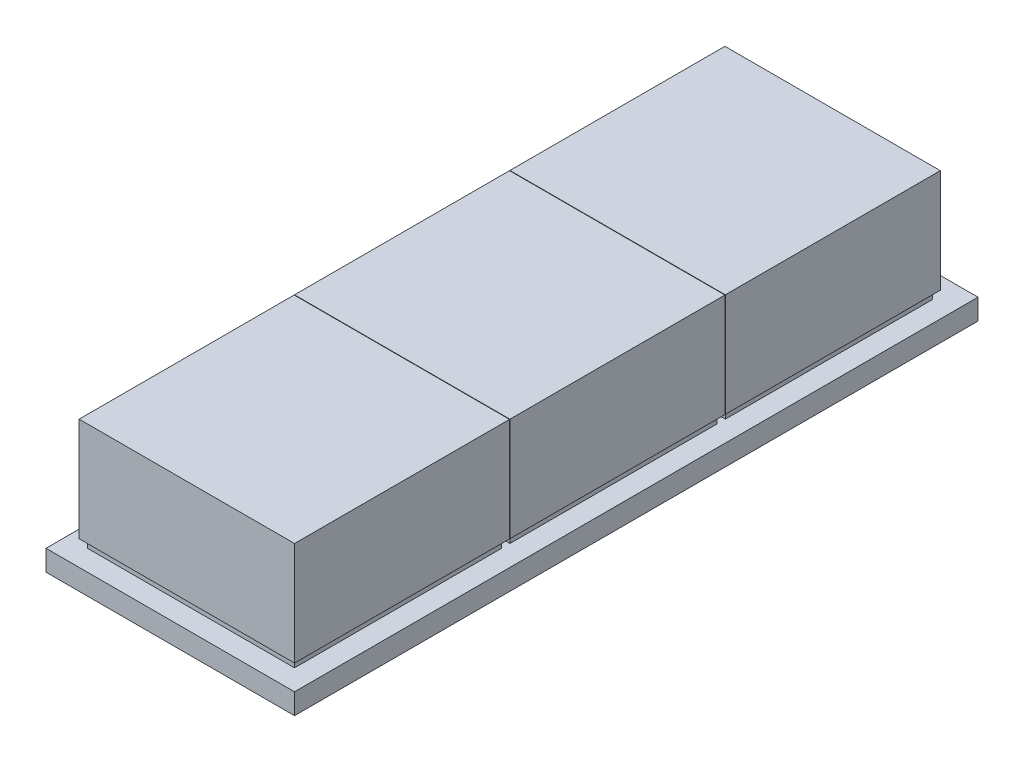
SolidWorks part; units mm, degrees
ref_plane "Front Plane" through (0, 0, 0) normal (0, 0, 1) x (1, 0, 0)
ref_plane "Top Plane" through (0, 0, 0) normal (0, 1, 0) x (1, 0, 0)
ref_plane "Right Plane" through (0, 0, 0) normal (1, 0, 0) x (0, 0, -1)
sketch "Sketch1" plane through (0, 0, 0) normal (0, 1, 0) x (1, 0, 0)
  line L1 (-30, -82.5) -> (30, -82.5)
  line L2 (-30, -82.5) -> (-30, 82.5)
  line L3 (-30, 82.5) -> (30, 82.5)
  line L4 (30, -82.5) -> (30, 82.5)
  line L5 (-30, -82.5) -> (30, 82.5) construction
  line L6 (-30, 82.5) -> (30, -82.5) construction
  point P0 (0, 0)
  dimension "D1" = 60
  dimension "D2" = 165
extrude "Boss-Extrude1" add sketch "Sketch1" along normal blind 5
sketch "Sketch2" plane through (0, 5, 0) normal (0, 1, 0) x (1, 0, 0)
  line L0 (0, 0) -> (0, -82.5) construction
  line L1 (-30, -82.5) -> (30, -82.5) construction
  line L3 (-25, -27.5) -> (25, -27.5)
  line L4 (-25, -27.5) -> (-25, -77.5)
  line L5 (-25, -77.5) -> (25, -77.5)
  line L6 (25, -27.5) -> (25, -77.5)
  line L7 (-25, -27.5) -> (25, -77.5) construction
  line L8 (-25, -77.5) -> (25, -27.5) construction
  point P5 (0, -52.5)
  dimension "D1" = 50
  dimension "D2" = 50
  dimension "D3" = 5
extrude "Boss-Extrude3" add sketch "Sketch2" along normal blind 2
pattern_linear "LPattern1" count 3 spacing 52 along (0, 0, -1) of "Boss-Extrude3"
sketch "Sketch3" plane through (0, 7, 0) normal (0, 1, 0) x (1, 0, 0)
  line L0 (0, 0) -> (0, -77.5) construction
  line L1 (-25, -77.5) -> (25, -77.5) construction
  line L3 (-26, -26.6) -> (26, -26.6)
  line L4 (-26, -26.6) -> (-26, -78.5)
  line L5 (-26, -78.5) -> (26, -78.5)
  line L6 (26, -26.6) -> (26, -78.5)
  line L7 (-26, -26.6) -> (26, -78.5) construction
  line L8 (-26, -78.5) -> (26, -26.6) construction
  line L9 (-30, -82.5) -> (30, -82.5) construction
  point P5 (0, -52.55)
  dimension "D1" = 52
  dimension "D2" = 51.9
  dimension "D3" = 4
extrude "Boss-Extrude8" add sketch "Sketch3" along normal blind 25
pattern_linear "LPattern5" count 3 spacing 52 along (0, 0, -1) of "Boss-Extrude8"
